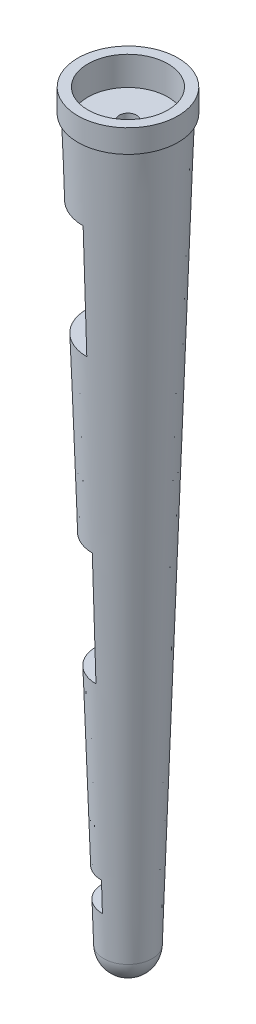
SolidWorks part; units mm, degrees
material "Natural Rubber"
ref_plane "Front Plane" through (0, 0, 0) normal (0, 0, 1) x (1, 0, 0)
ref_plane "Top Plane" through (0, 0, 0) normal (0, 1, 0) x (1, 0, 0)
ref_plane "Right Plane" through (0, 0, 0) normal (1, 0, 0) x (0, 0, -1)
sketch "Sketch1" plane through (0, 0, 0) normal (0, 0, 1) x (1, 0, 0)
  line L0 (-10.414, 11.321) -> (10.414, 11.321)
  line L1 (-10.414, 11.321) -> (-5.3581, -147.429)
  line L2 (0, 11.321) -> (0, 25.1345)
  line L3 (10.414, 11.321) -> (5.3581, -147.429)
  line L4 (0, 11.321) -> (0, -152.6193)
  arc A0 (5.3581, -147.429) -> (-5.3581, -147.429) centre (0, -147.2584) cw
  point P2 (0, 11.321)
  dimension "D1" = 20.828
  dimension "D2" = 158.75
  dimension "D3" = 5.3581
  dimension "D4" = 11.321
  dimension "D5" = 25.1345
revolve "Revolve1" add sketch "Sketch1" angle 360 about L4
sketch "Sketch2" plane through (0, 11.321, 0) normal (0, 1, 0) x (1, 0, 0)
  circle A2 centre (0, 0) radius 11.049
  circle A3 centre (0, 0) radius 11.049
  circle A4 centre (0, 0) radius 10.414
  circle A5 centre (0, 0) radius 10.414
  circle M3 centre (0, 0) radius 10.414
  dimension "D1" = 0.635
  dimension "D2" = 0
extrude "Boss-Extrude1" add sketch "Sketch2" along normal blind 5.08 contours M3 | A3 M3
sketch "Sketch3" plane through (0, 16.401, 0) normal (0, 1, 0) x (1, 0, 0)
  circle A0 centre (0, 0) radius 8.8265
  dimension "D1" = 17.653
sketch "Sketch5" plane through (0, 0, 0) normal (1, 0, 0) x (0, 0, -1)
  line L0 (-14.1248, -5.189) -> (-14.1248, -30.589)
  line L1 (-14.1248, -5.189) -> (3.6552, -5.189)
  line L2 (-14.1248, -30.589) -> (3.6552, -30.589)
  line L3 (3.6552, -5.189) -> (3.6552, -30.589)
  line L4 (0, 0) -> (0, 27.9478)
  line L5 (-14.1248, -68.689) -> (3.6552, -68.689)
  line L6 (-14.1248, -68.689) -> (-14.1248, -94.089)
  line L7 (-14.1248, -94.089) -> (3.6552, -94.089)
  line L8 (3.6552, -68.689) -> (3.6552, -94.089)
  line L9 (-14.1248, -132.189) -> (3.6552, -132.189)
  line L10 (-14.1248, -132.189) -> (-14.1248, -157.589)
  line L11 (-14.1248, -157.589) -> (3.6552, -157.589)
  line L12 (3.6552, -132.189) -> (3.6552, -157.589)
  line L13 (-14.1248, -138.6795) -> (3.6552, -138.6795)
  dimension "D1" = 25.4
  dimension "D2" = 17.78
  dimension "D3" = 3
extrude "Cut-Extrude2" cut sketch "Sketch5" against normal through all contours L3 L1 L0 L2 | L8 L5 L6 L7 | L10 L13 L12 L9
extrude "Cut-Extrude3" cut sketch "Sketch3" against normal blind 6.35
sketch "Sketch6" plane through (0, 10.051, 0) normal (0, 1, 0) x (1, 0, 0)
  circle A0 centre (0, 0) radius 1.905
  dimension "D1" = 3.81
extrude "Cut-Extrude4" cut sketch "Sketch6" against normal through all both and the other way through all
